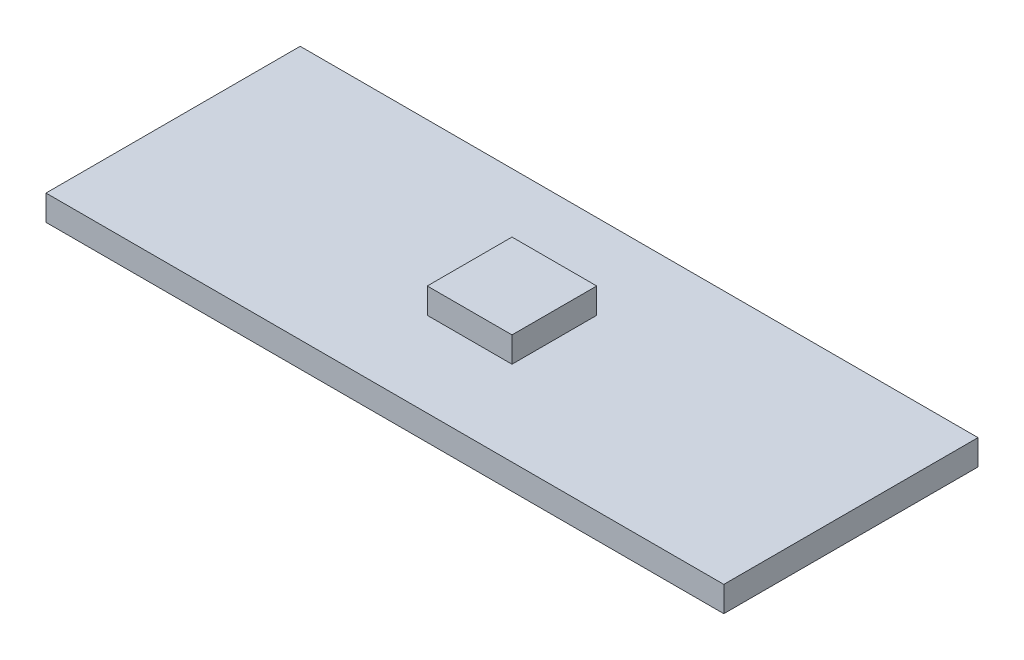
SolidWorks part; units mm, degrees
ref_plane "前视基准面" through (0, 0, 0) normal (0, 0, 1) x (1, 0, 0)
ref_plane "上视基准面" through (0, 0, 0) normal (0, 1, 0) x (1, 0, 0)
ref_plane "右视基准面" through (0, 0, 0) normal (1, 0, 0) x (0, 0, -1)
other "Configuration Table"
sketch "草图1" plane through (0, 0, 0) normal (0, 1, 0) x (1, 0, 0)
  line L1 (-20, -7.5) -> (20, -7.5)
  line L2 (-20, -7.5) -> (-20, 7.5)
  line L3 (-20, 7.5) -> (20, 7.5)
  line L4 (20, -7.5) -> (20, 7.5)
  line L5 (-20, -7.5) -> (20, 7.5) construction
  line L6 (-20, 7.5) -> (20, -7.5) construction
  point P0 (0, 0)
  dimension "D1" = 15
  dimension "D2" = 40
extrude "凸台-拉伸1" add sketch "草图1" along normal blind 1.5
sketch "草图2" plane through (0, 1.5, 0) normal (0, 1, 0) x (1, 0, 0)
  line L1 (-2.5, 2.5) -> (2.5, 2.5)
  line L2 (-2.5, 2.5) -> (-2.5, -2.5)
  line L3 (-2.5, -2.5) -> (2.5, -2.5)
  line L4 (2.5, 2.5) -> (2.5, -2.5)
  line L5 (-2.5, 2.5) -> (2.5, -2.5) construction
  line L6 (-2.5, -2.5) -> (2.5, 2.5) construction
  point P0 (0, 0)
  dimension "D1" = 5
  dimension "D2" = 5
extrude "凸台-拉伸2" add sketch "草图2" along normal blind 1.5
